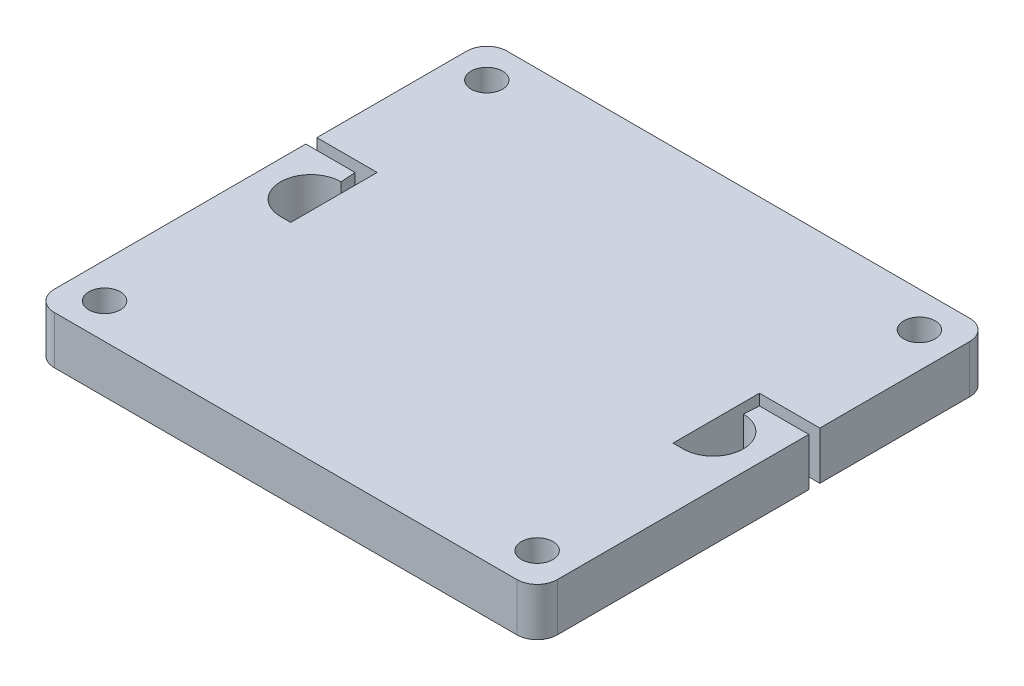
SolidWorks part; units mm, degrees
ref_plane "Front Plane" through (0, 0, 0) normal (0, 0, 1) x (1, 0, 0)
ref_plane "Top Plane" through (0, 0, 0) normal (0, 1, 0) x (1, 0, 0)
ref_plane "Right Plane" through (0, 0, 0) normal (1, 0, 0) x (0, 0, -1)
sketch "Sketch1" plane through (0, 0, 0) normal (0, 1, 0) x (1, 0, 0)
  line L0 (-17.5, -22.5) -> (17.5, 22.5) construction
  line L1 (-17.5, 22.5) -> (17.5, 22.5) construction
  line L2 (-17.5, 22.5) -> (-17.5, -22.5) construction
  line L3 (-17.5, -22.5) -> (17.5, -22.5) construction
  line L4 (17.5, 22.5) -> (17.5, -22.5) construction
  line L5 (0, 0) -> (0, 22.5) construction
  line L6 (-25, 22.5) -> (25, 22.5)
  line L7 (-25, 22.5) -> (-25, -22.5)
  line L8 (-25, -22.5) -> (25, -22.5)
  line L9 (25, 22.5) -> (25, -22.5)
  line L10 (0, 0) -> (-25, 0) construction
  circle A0 centre (-21.5, 19) radius 1.5625
  circle A1 centre (21.5, 19) radius 1.5625
  circle A2 centre (21.5, -19) radius 1.5625
  circle A3 centre (-21.5, -19) radius 1.5625
  dimension "D5" = 3.125
  dimension "D1" = 45
  dimension "D2" = 35
  dimension "D3" = 45
  dimension "D4" = 50
  dimension "D6" = 19
  dimension "D7" = 21.5
extrude "Boss-Extrude1" add sketch "Sketch1" along normal blind 4.7625
fillet "Fillet1" radius 2 4 edges at (-25, 2.3813, -22.5) (-25, 2.3813, 22.5) (25, 2.3813, -22.5) (25, 2.3813, 22.5)
sketch "Sketch2" plane through (0, 4.7625, 0) normal (0, 1, 0) x (1, 0, 0)
  line L0 (-25, 20.5) -> (-25, -20.5) construction
  line L1 (-25, 5.6) -> (-19, 5.6)
  line L2 (-25, 5.6) -> (-25, 4.5)
  line L3 (-20, -3) -> (-19, -3)
  line L4 (-19, 5.6) -> (-19, -3)
  line L7 (-20, 3) -> (-20.1, 4.5)
  line L8 (-20.1, 4.5) -> (-25, 4.5)
  arc A0 (-20, -3) -> (-20, 3) centre (-20, 0) cw
  dimension "D3" = 3
  dimension "D1" = 1.1
  dimension "D2" = 1.1
  dimension "D4" = 20
  dimension "D5" = 4.5
  dimension "D6" = 6
  dimension "D7" = 1
extrude "Cut-Extrude1" cut sketch "Sketch2" against normal through all
mirror "Mirror1" about plane through (0, 0, 0) normal (1, 0, 0) of "Cut-Extrude1"
